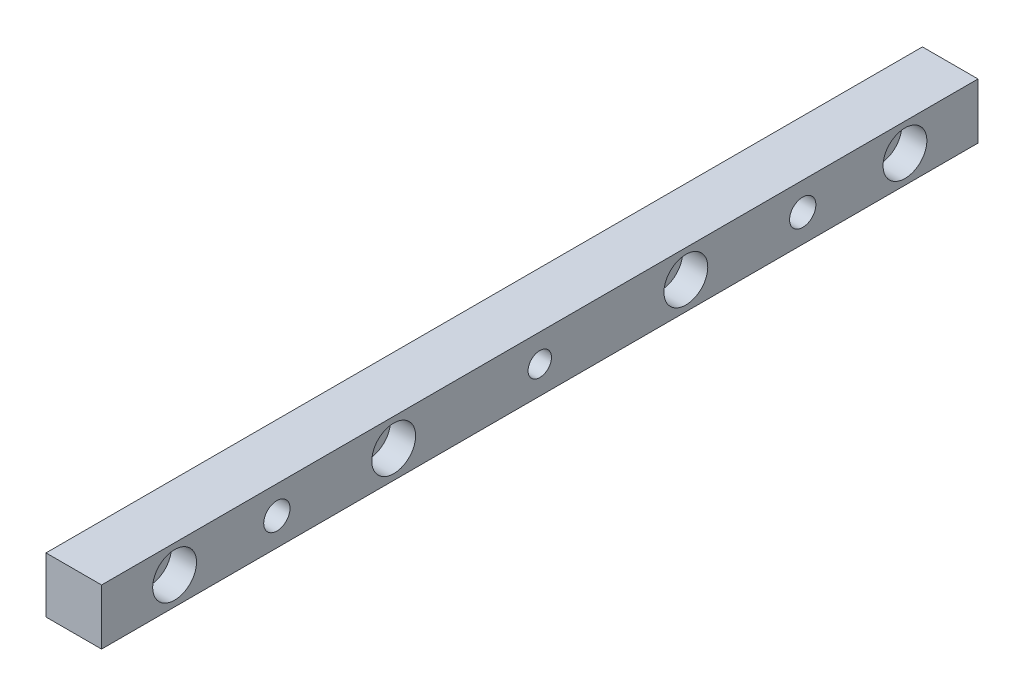
SolidWorks part; units mm, degrees
material "AISI 1020"
ref_plane "Plano frontal" through (0, 0, 0) normal (0, 0, 1) x (1, 0, 0)
ref_plane "Plano superior" through (0, 0, 0) normal (0, 1, 0) x (1, 0, 0)
ref_plane "Plano direito" through (0, 0, 0) normal (1, 0, 0) x (0, 0, -1)
sketch "Esboço1" plane through (0, 0, 0) normal (1, 0, 0) x (0, 0, -1)
  line L1 (-150, -6.32) -> (150, -6.32)
  line L2 (-150, -6.32) -> (-150, 12.7)
  line L3 (-150, 12.7) -> (150, 12.7)
  line L4 (150, -6.32) -> (150, 12.7)
  circle A0 centre (-50, 3.19) radius 4
  circle A1 centre (-125, 3.19) radius 4
  circle A2 centre (50, 3.19) radius 4
  circle A3 centre (125, 3.19) radius 4
  point P0 (0, 3.19)
  dimension "D3" = 250
  dimension "D4" = 100
  dimension "D5" = 75
  dimension "D7" = 8
  dimension "D8" = 8
  dimension "D9" = 8
  dimension "D10" = 8
  dimension "D11" = 9.51
  dimension "D12" = 9.51
  dimension "D13" = 9.51
  dimension "D14" = 9.51
  dimension "D1" = 19.02
  dimension "D2" = 300
  dimension "D6" = 50
extrude "Ressalto-extrusão1" add sketch "Esboço1" along normal blind 19.02
hole_wizard "Rebaixo para parafuso Allen sextavado de M81" positions "3DSketch2" profile "Esboço3" counterbore size "M8" standard "ISO" end condition through all
sketch3d "3DSketch2"
  line L0 (19.02, 3.19, 125) -> (0, 3.19, 125) construction
  line L1 (19.02, 3.19, 50) -> (0, 3.19, 50) construction
  line L2 (19.02, 3.19, -50) -> (0, 3.19, -50) construction
  line L3 (19.02, 3.19, -125) -> (0, 3.19, -125) construction
  point P0 (19.02, 3.19, 125)
  point P4 (19.02, 3.19, 50)
  point P8 (19.02, 3.19, -50)
  point P12 (19.02, 3.19, -125)
sketch "Esboço3" plane through (19.02, 3.19, 125) normal (0, 1, 0) x (0, 0, -1)
  line L0 (0, 0) -> (0, 19.02)
  line L1 (0, 19.02) -> (4.5, 19.02)
  line L3 (4.5, 19.02) -> (4.5, 8.6)
  line L4 (4.5, 8.6) -> (7.5, 8.6)
  line L5 (7.5, 8.6) -> (7.5, 0)
  line L7 (7.5, 0) -> (0, 0)
  line L11 (0, -6.35) -> (0, 107.95) construction
  dimension "Thru Hole Dia." = 9
  dimension "Thru Hole Depth" = 19.02
  dimension "C'Bore Dia." = 15
  dimension "C'Bore Depth" = 8.6
cosmetic thread "Representação de rosca2" parameters "D2"=12
cosmetic thread "Representação de rosca4" parameters "D2"=12
cosmetic thread "Representação de rosca5" parameters "D2"=12
cosmetic thread "Representação de rosca7" parameters "D2"=12
sketch "Esboço5" plane through (0, 0, 0) normal (-1, 0, 0) x (0, 0, 1)
  line L0 (-150, 12.7) -> (150, 12.7) construction
  line L2 (-150, 12.7) -> (150, 12.7) construction
  circle A0 centre (0, 3.19) radius 4
  circle A3 centre (90, 3.19) radius 4
  circle A4 centre (-90, 3.19) radius 4
  dimension "D1" = 90
  dimension "D2" = 90
  dimension "D3" = 9.51
  dimension "D4" = 9.51
  dimension "D5" = 9.51
extrude "Corte-extrusão1" cut sketch "Esboço5" against normal through all
cosmetic thread "Representação de rosca1" parameters "D2"=10
hole_wizard "Rebaixo para parafuso Allen sextavado de M82" positions "3DSketch8" profile "Esboço10" counterbore size "M8" standard "ISO"
sketch3d "3DSketch8"
  line L0 (19.02, 3.19, -90) -> (0, 3.19, -90) construction
  line L1 (19.02, 3.19, 90) -> (0, 3.19, 90) construction
  line L2 (19.02, 3.19, 0) -> (0, 3.19, 0) construction
  point P0 (0, 3.19, -90)
  point P4 (0, 3.19, 0)
  point P7 (0, 3.19, 90)
  point P11 (0, 3.19, 0)
  point P15 (0, 3.19, 0)
sketch "Esboço10" plane through (0, 3.19, -90) normal (0, 1, 0) x (0, 0, 1)
  line L0 (0, 0) -> (0, 19.02)
  line L1 (0, 19.02) -> (4.5, 19.02)
  line L3 (4.5, 19.02) -> (4.5, 8.6)
  line L4 (4.5, 8.6) -> (7.5, 8.6)
  line L5 (7.5, 8.6) -> (7.5, 0)
  line L7 (7.5, 0) -> (0, 0)
  line L11 (0, -6.35) -> (0, 107.95) construction
  dimension "Thru Hole Dia." = 9
  dimension "Thru Hole Depth" = 19.02
  dimension "C'Bore Dia." = 15
  dimension "C'Bore Depth" = 8.6
cosmetic thread "Representação de rosca3" parameters "D2"=12
cosmetic thread "Representação de rosca6" parameters "D2"=12
sketch "Esboço11" plane through (0, 0, 0) normal (-1, 0, 0) x (0, 0, 1)
  circle A0 centre (0, 3.19) radius 7.5
  dimension "D1" = 15
extrude "Corte-extrusão2" cut sketch "Esboço11" against normal blind 8.6
thread "Rosca1" pitch 1.25 start angle 0, offset 0, length 9, pitch 1.25, diameter 9
ref_plane "Plano2" through (0, 3.19, -129.5) normal (0, -1, 0) x (0, 0, -1)
sketch "Perfil da rosca2" plane through (0, 3.19, -129.5) normal (0, -1, 0) x (0, 0, -1)
  line L0 (0, 0) -> (0, 1.25) construction
  line L11 (0, 0) -> (0, 1.0937)
  line L12 (0, 1.0937) -> (-0.6766, 0.7031)
  line L13 (-0.6766, 0.7031) -> (-0.6766, 0.3906)
  line L15 (-0.6766, 0.3906) -> (0, 0)
  line L17 (-0.6766, 0.5469) -> (0, 0.5469) construction
  point P2 (0, 0)
  dimension "Pitch" = 1.25
  dimension "Profile_Angle" = 60
  dimension "Profile_Land" = 0.3125
  dimension "Profile_Height" = 0.6766
thread "Rosca2" pitch 1.25 start angle 0, offset 0, length 9, pitch 1.25, diameter 9
ref_plane "Plano3" through (19.02, 3.19, -85.5) normal (0, -1, 0) x (0, 0, 1)
sketch "Perfil da rosca3" plane through (19.02, 3.19, -85.5) normal (0, -1, 0) x (0, 0, 1)
  line L0 (0, 0) -> (0, 1.25) construction
  line L11 (0, 0) -> (0, 1.0937)
  line L12 (0, 1.0937) -> (-0.6766, 0.7031)
  line L13 (-0.6766, 0.7031) -> (-0.6766, 0.3906)
  line L15 (-0.6766, 0.3906) -> (0, 0)
  line L17 (-0.6766, 0.5469) -> (0, 0.5469) construction
  point P2 (0, 0)
  dimension "Pitch" = 1.25
  dimension "Profile_Angle" = 60
  dimension "Profile_Land" = 0.3125
  dimension "Profile_Height" = 0.6766
thread "Rosca3" pitch 1.25 start angle 0, offset 0, length 9, pitch 1.25, diameter 9
ref_plane "Plano4" through (10.42, 3.19, -45.5) normal (0, -1, 0) x (0, 0, 1)
sketch "Perfil da rosca4" plane through (10.42, 3.19, -45.5) normal (0, -1, 0) x (0, 0, 1)
  line L0 (0, 0) -> (0, 1.25) construction
  line L11 (0, 0) -> (0, 1.0937)
  line L12 (0, 1.0937) -> (-0.6766, 0.7031)
  line L13 (-0.6766, 0.7031) -> (-0.6766, 0.3906)
  line L15 (-0.6766, 0.3906) -> (0, 0)
  line L17 (-0.6766, 0.5469) -> (0, 0.5469) construction
  point P2 (0, 0)
  dimension "Pitch" = 1.25
  dimension "Profile_Angle" = 60
  dimension "Profile_Land" = 0.3125
  dimension "Profile_Height" = 0.6766
thread "Rosca4" pitch 1.25 start angle 0, offset 0, length 9, pitch 1.25, diameter 8
ref_plane "Plano5" through (8.6, 3.19, -4) normal (0, -1, 0) x (0, 0, -1)
sketch "Perfil da rosca5" plane through (8.6, 3.19, -4) normal (0, -1, 0) x (0, 0, -1)
  line L0 (0, 0) -> (0, 1.25) construction
  line L11 (0, 0) -> (0, 1.0937)
  line L12 (0, 1.0937) -> (-0.6766, 0.7031)
  line L13 (-0.6766, 0.7031) -> (-0.6766, 0.3906)
  line L15 (-0.6766, 0.3906) -> (0, 0)
  line L17 (-0.6766, 0.5469) -> (0, 0.5469) construction
  point P2 (0, 0)
  dimension "Pitch" = 1.25
  dimension "Profile_Angle" = 60
  dimension "Profile_Land" = 0.3125
  dimension "Profile_Height" = 0.6766
thread "Rosca5" pitch 1.25 start angle 0, offset 0, length 11.9, pitch 1.25, diameter 9
ref_plane "Plano6" through (0, 3.19, 45.5) normal (0, -1, 0) x (0, 0, -1)
sketch "Perfil da rosca6" plane through (0, 3.19, 45.5) normal (0, -1, 0) x (0, 0, -1)
  line L0 (0, 0) -> (0, 1.25) construction
  line L11 (0, 0) -> (0, 1.0937)
  line L12 (0, 1.0937) -> (-0.6766, 0.7031)
  line L13 (-0.6766, 0.7031) -> (-0.6766, 0.3906)
  line L15 (-0.6766, 0.3906) -> (0, 0)
  line L17 (-0.6766, 0.5469) -> (0, 0.5469) construction
  point P2 (0, 0)
  dimension "Pitch" = 1.25
  dimension "Profile_Angle" = 60
  dimension "Profile_Land" = 0.3125
  dimension "Profile_Height" = 0.6766
thread "Rosca6" pitch 1.25 start angle 0, offset 0, length 9, pitch 1.25, diameter 9
ref_plane "Plano7" through (8.6, 3.19, 85.5) normal (0, -1, 0) x (0, 0, -1)
sketch "Perfil da rosca7" plane through (8.6, 3.19, 85.5) normal (0, -1, 0) x (0, 0, -1)
  line L0 (0, 0) -> (0, 1.25) construction
  line L11 (0, 0) -> (0, 1.0937)
  line L12 (0, 1.0937) -> (-0.6766, 0.7031)
  line L13 (-0.6766, 0.7031) -> (-0.6766, 0.3906)
  line L15 (-0.6766, 0.3906) -> (0, 0)
  line L17 (-0.6766, 0.5469) -> (0, 0.5469) construction
  point P2 (0, 0)
  dimension "Pitch" = 1.25
  dimension "Profile_Angle" = 60
  dimension "Profile_Land" = 0.3125
  dimension "Profile_Height" = 0.6766
thread "Rosca7" pitch 1.25 start angle 0, offset 0, length 9, pitch 1.25, diameter 9
ref_plane "Plano8" through (10.42, 3.19, 129.5) normal (0, -1, 0) x (0, 0, 1)
sketch "Perfil da rosca8" plane through (10.42, 3.19, 129.5) normal (0, -1, 0) x (0, 0, 1)
  line L0 (0, 0) -> (0, 1.25) construction
  line L11 (0, 0) -> (0, 1.0937)
  line L12 (0, 1.0937) -> (-0.6766, 0.7031)
  line L13 (-0.6766, 0.7031) -> (-0.6766, 0.3906)
  line L15 (-0.6766, 0.3906) -> (0, 0)
  line L17 (-0.6766, 0.5469) -> (0, 0.5469) construction
  point P2 (0, 0)
  dimension "Pitch" = 1.25
  dimension "Profile_Angle" = 60
  dimension "Profile_Land" = 0.3125
  dimension "Profile_Height" = 0.6766
